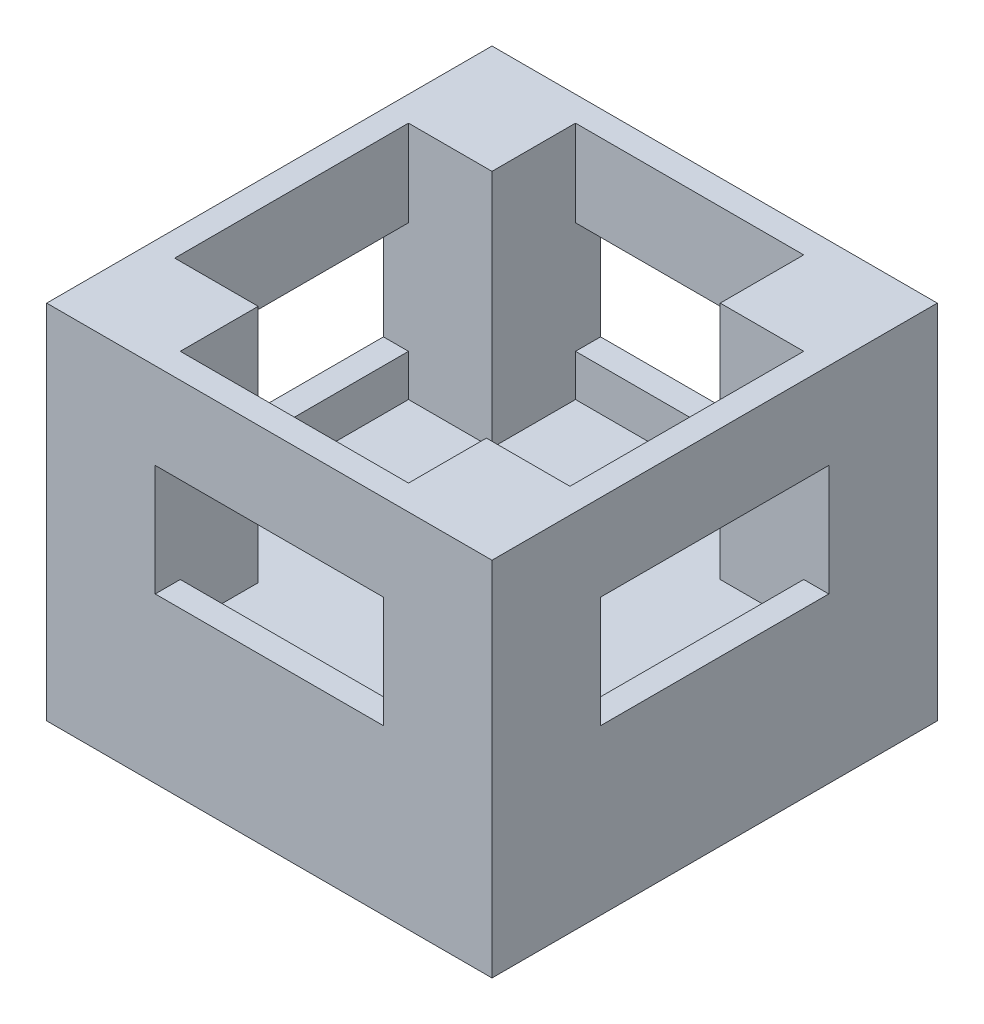
SolidWorks part; units mm, degrees
ref_plane "Front Plane" through (0, 0, 0) normal (0, 0, 1) x (1, 0, 0)
ref_plane "Top Plane" through (0, 0, 0) normal (0, 1, 0) x (1, 0, 0)
ref_plane "Right Plane" through (0, 0, 0) normal (1, 0, 0) x (0, 0, -1)
sketch "Sketch1" plane through (0, 0, 0) normal (0, 1, 0) x (1, 0, 0)
  line L1 (0, 0) -> (10.16, 0)
  line L2 (0, 0) -> (0, 10.16)
  line L3 (0, 10.16) -> (10.16, 10.16)
  line L4 (10.16, 0) -> (10.16, 10.16)
extrude "Boss-Extrude1" add sketch "Sketch1" along normal blind 8.255
sketch "Sketch2" plane through (0, 0, 0) normal (0, 0, 1) x (1, 0, 0)
  line L1 (2.4765, 2.794) -> (7.6835, 2.794)
  line L2 (2.4765, 2.794) -> (2.4765, 7.239)
  line L3 (2.4765, 7.239) -> (7.6835, 7.239)
  line L4 (7.6835, 2.794) -> (7.6835, 7.239)
  line L6 (3.302, 6.2865) -> (6.858, 6.2865)
  line L7 (3.302, 6.2865) -> (3.302, 3.7465)
  line L8 (3.302, 3.7465) -> (6.858, 3.7465)
  line L9 (6.858, 6.2865) -> (6.858, 3.7465)
extrude "Cut-Extrude3" cut sketch "Sketch2" against normal blind 10.16 contours L6 L9 L8 L7
sketch "Sketch4" plane through (0, 0, 0) normal (0, 0, 1) x (1, 0, 0)
  line L1 (2.4765, 2.794) -> (7.6835, 2.794)
  line L2 (2.4765, 2.794) -> (2.4765, 8.255)
  line L3 (2.4765, 8.255) -> (7.6835, 8.255)
  line L4 (7.6835, 2.794) -> (7.6835, 8.255)
extrude "Cut-Extrude4" cut sketch "Sketch4" against normal blind 9.017 from offset 0.5715 offset against normal yes
sketch "Sketch5" plane through (10.16, 0, 0) normal (1, 0, 0) x (0, 0, -1)
  line L1 (2.3495, 2.794) -> (7.6835, 2.794)
  line L2 (2.3495, 2.794) -> (2.3495, 8.255)
  line L3 (2.3495, 8.255) -> (7.6835, 8.255)
  line L4 (7.6835, 2.794) -> (7.6835, 8.255)
extrude "Cut-Extrude5" cut sketch "Sketch5" against normal blind 9.017 from offset 0.5715 offset against normal yes
sketch "Sketch6" plane through (10.16, 0, 0) normal (1, 0, 0) x (0, 0, -1)
  line L1 (3.302, 6.2865) -> (6.858, 6.2865)
  line L2 (3.302, 6.2865) -> (3.302, 3.7465)
  line L3 (3.302, 3.7465) -> (6.858, 3.7465)
  line L4 (6.858, 6.2865) -> (6.858, 3.7465)
extrude "Cut-Extrude6" cut sketch "Sketch6" against normal blind 10.16
sketch "Sketch7" plane through (0, 0, 0) normal (0, 0, 1) x (1, 0, 0)
  line L1 (2.4765, 6.2865) -> (7.6835, 6.2865)
  line L2 (2.4765, 6.2865) -> (2.4765, 3.7465)
  line L3 (2.4765, 3.7465) -> (7.6835, 3.7465)
  line L4 (7.6835, 6.2865) -> (7.6835, 3.7465)
extrude "Cut-Extrude7" cut sketch "Sketch7" against normal blind 10.16
sketch "Sketch8" plane through (10.16, 0, 0) normal (1, 0, 0) x (0, 0, -1)
  line L1 (2.4765, 6.2865) -> (7.6835, 6.2865)
  line L2 (2.4765, 6.2865) -> (2.4765, 3.7465)
  line L3 (2.4765, 3.7465) -> (7.6835, 3.7465)
  line L4 (7.6835, 6.2865) -> (7.6835, 3.7465)
extrude "Cut-Extrude8" cut sketch "Sketch8" against normal blind 10.16
